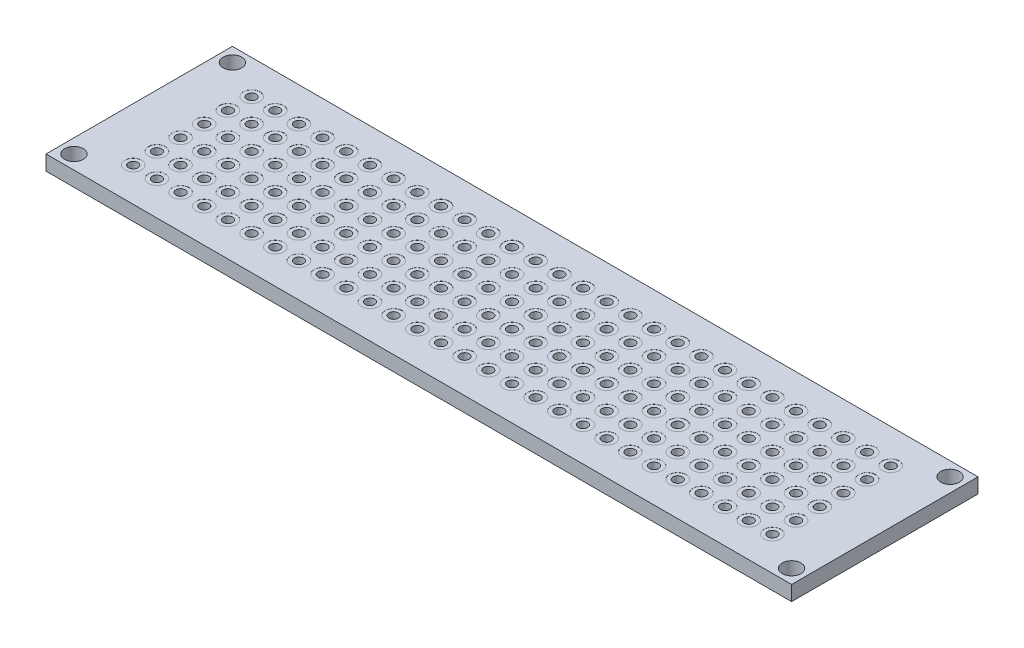
SolidWorks part; units mm, degrees
ref_plane "Front Plane" through (0, 0, 0) normal (0, 0, 1) x (1, 0, 0)
ref_plane "Top Plane" through (0, 0, 0) normal (0, 1, 0) x (1, 0, 0)
ref_plane "Right Plane" through (0, 0, 0) normal (1, 0, 0) x (0, 0, -1)
sketch "Sketch1" plane through (0, 0, 0) normal (0, 1, 0) x (1, 0, 0)
  line L0 (40, 0) -> (40, 20) construction
  line L1 (0, 0) -> (80, 0)
  line L2 (0, 0) -> (0, 20)
  line L3 (0, 20) -> (80, 20)
  line L4 (80, 0) -> (80, 20)
  line L5 (0, 10) -> (80, 10) construction
  circle A0 centre (5.71, 16.35) radius 0.5
  circle A1 centre (5.71, 13.81) radius 0.5
  circle A2 centre (5.71, 11.27) radius 0.5
  circle A3 centre (5.71, 8.73) radius 0.5
  circle A4 centre (5.71, 6.19) radius 0.5
  circle A5 centre (5.71, 3.65) radius 0.5
  circle A6 centre (8.25, 16.35) radius 0.5
  circle A7 centre (8.25, 13.81) radius 0.5
  circle A8 centre (8.25, 11.27) radius 0.5
  circle A9 centre (8.25, 8.73) radius 0.5
  circle A10 centre (8.25, 6.19) radius 0.5
  circle A11 centre (8.25, 3.65) radius 0.5
  circle A12 centre (10.79, 16.35) radius 0.5
  circle A13 centre (10.79, 13.81) radius 0.5
  circle A14 centre (10.79, 11.27) radius 0.5
  circle A15 centre (10.79, 8.73) radius 0.5
  circle A16 centre (10.79, 6.19) radius 0.5
  circle A17 centre (10.79, 3.65) radius 0.5
  circle A18 centre (13.33, 16.35) radius 0.5
  circle A19 centre (13.33, 13.81) radius 0.5
  circle A20 centre (13.33, 11.27) radius 0.5
  circle A21 centre (13.33, 8.73) radius 0.5
  circle A22 centre (13.33, 6.19) radius 0.5
  circle A23 centre (13.33, 3.65) radius 0.5
  circle A24 centre (15.87, 16.35) radius 0.5
  circle A25 centre (15.87, 13.81) radius 0.5
  circle A26 centre (15.87, 11.27) radius 0.5
  circle A27 centre (15.87, 8.73) radius 0.5
  circle A28 centre (15.87, 6.19) radius 0.5
  circle A29 centre (15.87, 3.65) radius 0.5
  circle A30 centre (18.41, 16.35) radius 0.5
  circle A31 centre (18.41, 13.81) radius 0.5
  circle A32 centre (18.41, 11.27) radius 0.5
  circle A33 centre (18.41, 8.73) radius 0.5
  circle A34 centre (18.41, 6.19) radius 0.5
  circle A35 centre (18.41, 3.65) radius 0.5
  circle A36 centre (20.95, 16.35) radius 0.5
  circle A37 centre (20.95, 13.81) radius 0.5
  circle A38 centre (20.95, 11.27) radius 0.5
  circle A39 centre (20.95, 8.73) radius 0.5
  circle A40 centre (20.95, 6.19) radius 0.5
  circle A41 centre (20.95, 3.65) radius 0.5
  circle A42 centre (23.49, 16.35) radius 0.5
  circle A43 centre (23.49, 13.81) radius 0.5
  circle A44 centre (23.49, 11.27) radius 0.5
  circle A45 centre (23.49, 8.73) radius 0.5
  circle A46 centre (23.49, 6.19) radius 0.5
  circle A47 centre (23.49, 3.65) radius 0.5
  circle A48 centre (26.03, 16.35) radius 0.5
  circle A49 centre (26.03, 13.81) radius 0.5
  circle A50 centre (26.03, 11.27) radius 0.5
  circle A51 centre (26.03, 8.73) radius 0.5
  circle A52 centre (26.03, 6.19) radius 0.5
  circle A53 centre (26.03, 3.65) radius 0.5
  circle A54 centre (28.57, 16.35) radius 0.5
  circle A55 centre (28.57, 13.81) radius 0.5
  circle A56 centre (28.57, 11.27) radius 0.5
  circle A57 centre (28.57, 8.73) radius 0.5
  circle A58 centre (28.57, 6.19) radius 0.5
  circle A59 centre (28.57, 3.65) radius 0.5
  circle A60 centre (31.11, 16.35) radius 0.5
  circle A61 centre (31.11, 13.81) radius 0.5
  circle A62 centre (31.11, 11.27) radius 0.5
  circle A63 centre (31.11, 8.73) radius 0.5
  circle A64 centre (31.11, 6.19) radius 0.5
  circle A65 centre (31.11, 3.65) radius 0.5
  circle A66 centre (33.65, 16.35) radius 0.5
  circle A67 centre (33.65, 13.81) radius 0.5
  circle A68 centre (33.65, 11.27) radius 0.5
  circle A69 centre (33.65, 8.73) radius 0.5
  circle A70 centre (33.65, 6.19) radius 0.5
  circle A71 centre (33.65, 3.65) radius 0.5
  circle A72 centre (36.19, 16.35) radius 0.5
  circle A73 centre (36.19, 13.81) radius 0.5
  circle A74 centre (36.19, 11.27) radius 0.5
  circle A75 centre (36.19, 8.73) radius 0.5
  circle A76 centre (36.19, 6.19) radius 0.5
  circle A77 centre (36.19, 3.65) radius 0.5
  circle A78 centre (38.73, 16.35) radius 0.5
  circle A79 centre (38.73, 13.81) radius 0.5
  circle A80 centre (38.73, 11.27) radius 0.5
  circle A81 centre (38.73, 8.73) radius 0.5
  circle A82 centre (38.73, 6.19) radius 0.5
  circle A83 centre (38.73, 3.65) radius 0.5
  circle A84 centre (41.27, 16.35) radius 0.5
  circle A85 centre (41.27, 13.81) radius 0.5
  circle A86 centre (41.27, 11.27) radius 0.5
  circle A87 centre (41.27, 8.73) radius 0.5
  circle A88 centre (41.27, 6.19) radius 0.5
  circle A89 centre (41.27, 3.65) radius 0.5
  circle A90 centre (43.81, 16.35) radius 0.5
  circle A91 centre (43.81, 13.81) radius 0.5
  circle A92 centre (43.81, 11.27) radius 0.5
  circle A93 centre (43.81, 8.73) radius 0.5
  circle A94 centre (43.81, 6.19) radius 0.5
  circle A95 centre (43.81, 3.65) radius 0.5
  circle A96 centre (46.35, 16.35) radius 0.5
  circle A97 centre (46.35, 13.81) radius 0.5
  circle A98 centre (46.35, 11.27) radius 0.5
  circle A99 centre (46.35, 8.73) radius 0.5
  circle A100 centre (46.35, 6.19) radius 0.5
  circle A101 centre (46.35, 3.65) radius 0.5
  circle A102 centre (48.89, 16.35) radius 0.5
  circle A103 centre (48.89, 13.81) radius 0.5
  circle A104 centre (48.89, 11.27) radius 0.5
  circle A105 centre (48.89, 8.73) radius 0.5
  circle A106 centre (48.89, 6.19) radius 0.5
  circle A107 centre (48.89, 3.65) radius 0.5
  circle A108 centre (51.43, 16.35) radius 0.5
  circle A109 centre (51.43, 13.81) radius 0.5
  circle A110 centre (51.43, 11.27) radius 0.5
  circle A111 centre (51.43, 8.73) radius 0.5
  circle A112 centre (51.43, 6.19) radius 0.5
  circle A113 centre (51.43, 3.65) radius 0.5
  circle A114 centre (53.97, 16.35) radius 0.5
  circle A115 centre (53.97, 13.81) radius 0.5
  circle A116 centre (53.97, 11.27) radius 0.5
  circle A117 centre (53.97, 8.73) radius 0.5
  circle A118 centre (53.97, 6.19) radius 0.5
  circle A119 centre (53.97, 3.65) radius 0.5
  circle A120 centre (56.51, 16.35) radius 0.5
  circle A121 centre (56.51, 13.81) radius 0.5
  circle A122 centre (56.51, 11.27) radius 0.5
  circle A123 centre (56.51, 8.73) radius 0.5
  circle A124 centre (56.51, 6.19) radius 0.5
  circle A125 centre (56.51, 3.65) radius 0.5
  circle A126 centre (59.05, 16.35) radius 0.5
  circle A127 centre (59.05, 13.81) radius 0.5
  circle A128 centre (59.05, 11.27) radius 0.5
  circle A129 centre (59.05, 8.73) radius 0.5
  circle A130 centre (59.05, 6.19) radius 0.5
  circle A131 centre (59.05, 3.65) radius 0.5
  circle A132 centre (61.59, 16.35) radius 0.5
  circle A133 centre (61.59, 13.81) radius 0.5
  circle A134 centre (61.59, 11.27) radius 0.5
  circle A135 centre (61.59, 8.73) radius 0.5
  circle A136 centre (61.59, 6.19) radius 0.5
  circle A137 centre (61.59, 3.65) radius 0.5
  circle A138 centre (64.13, 16.35) radius 0.5
  circle A139 centre (64.13, 13.81) radius 0.5
  circle A140 centre (64.13, 11.27) radius 0.5
  circle A141 centre (64.13, 8.73) radius 0.5
  circle A142 centre (64.13, 6.19) radius 0.5
  circle A143 centre (64.13, 3.65) radius 0.5
  circle A144 centre (66.67, 16.35) radius 0.5
  circle A145 centre (66.67, 13.81) radius 0.5
  circle A146 centre (66.67, 11.27) radius 0.5
  circle A147 centre (66.67, 8.73) radius 0.5
  circle A148 centre (66.67, 6.19) radius 0.5
  circle A149 centre (66.67, 3.65) radius 0.5
  circle A150 centre (69.21, 16.35) radius 0.5
  circle A151 centre (69.21, 13.81) radius 0.5
  circle A152 centre (69.21, 11.27) radius 0.5
  circle A153 centre (69.21, 8.73) radius 0.5
  circle A154 centre (69.21, 6.19) radius 0.5
  circle A155 centre (69.21, 3.65) radius 0.5
  circle A156 centre (71.75, 16.35) radius 0.5
  circle A157 centre (71.75, 13.81) radius 0.5
  circle A158 centre (71.75, 11.27) radius 0.5
  circle A159 centre (71.75, 8.73) radius 0.5
  circle A160 centre (71.75, 6.19) radius 0.5
  circle A161 centre (71.75, 3.65) radius 0.5
  circle A162 centre (74.29, 16.35) radius 0.5
  circle A163 centre (74.29, 13.81) radius 0.5
  circle A164 centre (74.29, 11.27) radius 0.5
  circle A165 centre (74.29, 8.73) radius 0.5
  circle A166 centre (74.29, 6.19) radius 0.5
  circle A167 centre (74.29, 3.65) radius 0.5
  circle A168 centre (1.5, 18.5) radius 1
  circle A169 centre (78.5, 18.5) radius 1
  circle A170 centre (1.5, 1.5) radius 1
  circle A171 centre (78.5, 1.5) radius 1
  dimension "D3" = 1
  dimension "D8" = 2
  dimension "D9" = 0.5
  dimension "D10" = 0.5
  dimension "D1" = 80
  dimension "D2" = 20
  dimension "D5" = 2.54
  dimension "D7" = 2.54
  dimension "D4" = 6
  dimension "D6" = 28
extrude "Boss-Extrude1" add sketch "Sketch1" along normal blind 1.6
sketch "Sketch2" plane through (0, 1.6, 0) normal (0, 1, 0) x (1, 0, 0)
  circle A0 centre (5.71, 16.35) radius 0.9
  circle A1 centre (8.25, 16.35) radius 0.9
  circle A2 centre (10.79, 16.35) radius 0.9
  circle A3 centre (13.33, 16.35) radius 0.9
  circle A4 centre (15.87, 16.35) radius 0.9
  circle A5 centre (18.41, 16.35) radius 0.9
  circle A6 centre (20.95, 16.35) radius 0.9
  circle A7 centre (23.49, 16.35) radius 0.9
  circle A8 centre (26.03, 16.35) radius 0.9
  circle A9 centre (28.57, 16.35) radius 0.9
  circle A10 centre (31.11, 16.35) radius 0.9
  circle A11 centre (33.65, 16.35) radius 0.9
  circle A12 centre (36.19, 16.35) radius 0.9
  circle A13 centre (38.73, 16.35) radius 0.9
  circle A14 centre (41.27, 16.35) radius 0.9
  circle A15 centre (43.81, 16.35) radius 0.9
  circle A16 centre (46.35, 16.35) radius 0.9
  circle A17 centre (48.89, 16.35) radius 0.9
  circle A18 centre (51.43, 16.35) radius 0.9
  circle A19 centre (53.97, 16.35) radius 0.9
  circle A20 centre (56.51, 16.35) radius 0.9
  circle A21 centre (59.05, 16.35) radius 0.9
  circle A22 centre (61.59, 16.35) radius 0.9
  circle A23 centre (64.13, 16.35) radius 0.9
  circle A24 centre (66.67, 16.35) radius 0.9
  circle A25 centre (69.21, 16.35) radius 0.9
  circle A26 centre (71.75, 16.35) radius 0.9
  circle A27 centre (74.29, 16.35) radius 0.9
  circle A28 centre (8.25, 13.81) radius 0.9
  circle A29 centre (10.79, 13.81) radius 0.9
  circle A30 centre (13.33, 13.81) radius 0.9
  circle A31 centre (15.87, 13.81) radius 0.9
  circle A32 centre (18.41, 13.81) radius 0.9
  circle A33 centre (20.95, 13.81) radius 0.9
  circle A34 centre (23.49, 13.81) radius 0.9
  circle A35 centre (26.03, 13.81) radius 0.9
  circle A36 centre (28.57, 13.81) radius 0.9
  circle A37 centre (31.11, 13.81) radius 0.9
  circle A38 centre (33.65, 13.81) radius 0.9
  circle A39 centre (36.19, 13.81) radius 0.9
  circle A40 centre (38.73, 13.81) radius 0.9
  circle A41 centre (41.27, 13.81) radius 0.9
  circle A42 centre (43.81, 13.81) radius 0.9
  circle A43 centre (46.35, 13.81) radius 0.9
  circle A44 centre (48.89, 13.81) radius 0.9
  circle A45 centre (51.43, 13.81) radius 0.9
  circle A46 centre (53.97, 13.81) radius 0.9
  circle A47 centre (56.51, 13.81) radius 0.9
  circle A48 centre (59.05, 13.81) radius 0.9
  circle A49 centre (61.59, 13.81) radius 0.9
  circle A50 centre (64.13, 13.81) radius 0.9
  circle A51 centre (66.67, 13.81) radius 0.9
  circle A52 centre (69.21, 13.81) radius 0.9
  circle A53 centre (71.75, 13.81) radius 0.9
  circle A54 centre (74.29, 13.81) radius 0.9
  circle A55 centre (8.25, 11.27) radius 0.9
  circle A56 centre (10.79, 11.27) radius 0.9
  circle A57 centre (13.33, 11.27) radius 0.9
  circle A58 centre (15.87, 11.27) radius 0.9
  circle A59 centre (18.41, 11.27) radius 0.9
  circle A60 centre (20.95, 11.27) radius 0.9
  circle A61 centre (23.49, 11.27) radius 0.9
  circle A62 centre (26.03, 11.27) radius 0.9
  circle A63 centre (28.57, 11.27) radius 0.9
  circle A64 centre (31.11, 11.27) radius 0.9
  circle A65 centre (33.65, 11.27) radius 0.9
  circle A66 centre (36.19, 11.27) radius 0.9
  circle A67 centre (38.73, 11.27) radius 0.9
  circle A68 centre (41.27, 11.27) radius 0.9
  circle A69 centre (43.81, 11.27) radius 0.9
  circle A70 centre (46.35, 11.27) radius 0.9
  circle A71 centre (48.89, 11.27) radius 0.9
  circle A72 centre (51.43, 11.27) radius 0.9
  circle A73 centre (53.97, 11.27) radius 0.9
  circle A74 centre (56.51, 11.27) radius 0.9
  circle A75 centre (59.05, 11.27) radius 0.9
  circle A76 centre (61.59, 11.27) radius 0.9
  circle A77 centre (64.13, 11.27) radius 0.9
  circle A78 centre (66.67, 11.27) radius 0.9
  circle A79 centre (69.21, 11.27) radius 0.9
  circle A80 centre (71.75, 11.27) radius 0.9
  circle A81 centre (74.29, 11.27) radius 0.9
  circle A82 centre (8.25, 8.73) radius 0.9
  circle A83 centre (10.79, 8.73) radius 0.9
  circle A84 centre (13.33, 8.73) radius 0.9
  circle A85 centre (15.87, 8.73) radius 0.9
  circle A86 centre (18.41, 8.73) radius 0.9
  circle A87 centre (20.95, 8.73) radius 0.9
  circle A88 centre (23.49, 8.73) radius 0.9
  circle A89 centre (26.03, 8.73) radius 0.9
  circle A90 centre (28.57, 8.73) radius 0.9
  circle A91 centre (31.11, 8.73) radius 0.9
  circle A92 centre (33.65, 8.73) radius 0.9
  circle A93 centre (36.19, 8.73) radius 0.9
  circle A94 centre (38.73, 8.73) radius 0.9
  circle A95 centre (41.27, 8.73) radius 0.9
  circle A96 centre (43.81, 8.73) radius 0.9
  circle A97 centre (46.35, 8.73) radius 0.9
  circle A98 centre (48.89, 8.73) radius 0.9
  circle A99 centre (51.43, 8.73) radius 0.9
  circle A100 centre (53.97, 8.73) radius 0.9
  circle A101 centre (56.51, 8.73) radius 0.9
  circle A102 centre (59.05, 8.73) radius 0.9
  circle A103 centre (61.59, 8.73) radius 0.9
  circle A104 centre (64.13, 8.73) radius 0.9
  circle A105 centre (66.67, 8.73) radius 0.9
  circle A106 centre (69.21, 8.73) radius 0.9
  circle A107 centre (71.75, 8.73) radius 0.9
  circle A108 centre (74.29, 8.73) radius 0.9
  circle A109 centre (8.25, 6.19) radius 0.9
  circle A110 centre (10.79, 6.19) radius 0.9
  circle A111 centre (13.33, 6.19) radius 0.9
  circle A112 centre (15.87, 6.19) radius 0.9
  circle A113 centre (18.41, 6.19) radius 0.9
  circle A114 centre (20.95, 6.19) radius 0.9
  circle A115 centre (23.49, 6.19) radius 0.9
  circle A116 centre (26.03, 6.19) radius 0.9
  circle A117 centre (28.57, 6.19) radius 0.9
  circle A118 centre (31.11, 6.19) radius 0.9
  circle A119 centre (33.65, 6.19) radius 0.9
  circle A120 centre (36.19, 6.19) radius 0.9
  circle A121 centre (38.73, 6.19) radius 0.9
  circle A122 centre (41.27, 6.19) radius 0.9
  circle A123 centre (43.81, 6.19) radius 0.9
  circle A124 centre (46.35, 6.19) radius 0.9
  circle A125 centre (48.89, 6.19) radius 0.9
  circle A126 centre (51.43, 6.19) radius 0.9
  circle A127 centre (53.97, 6.19) radius 0.9
  circle A128 centre (56.51, 6.19) radius 0.9
  circle A129 centre (59.05, 6.19) radius 0.9
  circle A130 centre (61.59, 6.19) radius 0.9
  circle A131 centre (64.13, 6.19) radius 0.9
  circle A132 centre (66.67, 6.19) radius 0.9
  circle A133 centre (69.21, 6.19) radius 0.9
  circle A134 centre (71.75, 6.19) radius 0.9
  circle A135 centre (74.29, 6.19) radius 0.9
  circle A136 centre (8.25, 3.65) radius 0.9
  circle A137 centre (10.79, 3.65) radius 0.9
  circle A138 centre (13.33, 3.65) radius 0.9
  circle A139 centre (15.87, 3.65) radius 0.9
  circle A140 centre (18.41, 3.65) radius 0.9
  circle A141 centre (20.95, 3.65) radius 0.9
  circle A142 centre (23.49, 3.65) radius 0.9
  circle A143 centre (26.03, 3.65) radius 0.9
  circle A144 centre (28.57, 3.65) radius 0.9
  circle A145 centre (31.11, 3.65) radius 0.9
  circle A146 centre (33.65, 3.65) radius 0.9
  circle A147 centre (36.19, 3.65) radius 0.9
  circle A148 centre (38.73, 3.65) radius 0.9
  circle A149 centre (41.27, 3.65) radius 0.9
  circle A150 centre (43.81, 3.65) radius 0.9
  circle A151 centre (46.35, 3.65) radius 0.9
  circle A152 centre (48.89, 3.65) radius 0.9
  circle A153 centre (51.43, 3.65) radius 0.9
  circle A154 centre (53.97, 3.65) radius 0.9
  circle A155 centre (56.51, 3.65) radius 0.9
  circle A156 centre (59.05, 3.65) radius 0.9
  circle A157 centre (61.59, 3.65) radius 0.9
  circle A158 centre (64.13, 3.65) radius 0.9
  circle A159 centre (66.67, 3.65) radius 0.9
  circle A160 centre (69.21, 3.65) radius 0.9
  circle A161 centre (71.75, 3.65) radius 0.9
  circle A162 centre (74.29, 3.65) radius 0.9
  circle A163 centre (5.71, 13.81) radius 0.9
  circle A164 centre (5.71, 11.27) radius 0.9
  circle A165 centre (5.71, 8.73) radius 0.9
  circle A166 centre (5.71, 6.19) radius 0.9
  circle A167 centre (5.71, 3.65) radius 0.9
  dimension "D1" = 1.8
  dimension "D2" = 28
  dimension "D3" = 6
extrude "Cut-Extrude1" cut sketch "Sketch2" against normal blind 0.01
sketch "Sketch3" plane through (0, 0, 0) normal (0, -1, 0) x (1, 0, 0)
  circle A1 centre (20.95, -3.65) radius 0.9
  circle A2 centre (20.95, -3.65) radius 0.9
  circle A3 centre (18.41, -3.65) radius 0.9
  circle A4 centre (18.41, -3.65) radius 0.9
  circle A5 centre (15.87, -3.65) radius 0.9
  circle A6 centre (15.87, -3.65) radius 0.9
  circle A7 centre (13.33, -3.65) radius 0.9
  circle A8 centre (13.33, -3.65) radius 0.9
  circle A9 centre (10.79, -3.65) radius 0.9
  circle A10 centre (10.79, -3.65) radius 0.9
  circle A11 centre (8.25, -3.65) radius 0.9
  circle A12 centre (8.25, -3.65) radius 0.9
  circle A13 centre (74.29, -6.19) radius 0.9
  circle A14 centre (74.29, -6.19) radius 0.9
  circle A15 centre (71.75, -6.19) radius 0.9
  circle A16 centre (71.75, -6.19) radius 0.9
  circle A17 centre (18.41, -16.35) radius 0.9
  circle A18 centre (18.41, -16.35) radius 0.9
  circle A19 centre (15.87, -16.35) radius 0.9
  circle A20 centre (15.87, -16.35) radius 0.9
  circle A21 centre (13.33, -16.35) radius 0.9
  circle A22 centre (13.33, -16.35) radius 0.9
  circle A23 centre (10.79, -16.35) radius 0.9
  circle A24 centre (10.79, -16.35) radius 0.9
  circle A25 centre (8.25, -16.35) radius 0.9
  circle A26 centre (8.25, -16.35) radius 0.9
  circle A27 centre (5.71, -16.35) radius 0.9
  circle A28 centre (5.71, -16.35) radius 0.9
  circle A29 centre (41.27, -3.65) radius 0.9
  circle A30 centre (41.27, -3.65) radius 0.9
  circle A31 centre (38.73, -3.65) radius 0.9
  circle A32 centre (38.73, -3.65) radius 0.9
  circle A33 centre (36.19, -3.65) radius 0.9
  circle A34 centre (36.19, -3.65) radius 0.9
  circle A35 centre (33.65, -3.65) radius 0.9
  circle A36 centre (33.65, -3.65) radius 0.9
  circle A37 centre (31.11, -3.65) radius 0.9
  circle A38 centre (31.11, -3.65) radius 0.9
  circle A39 centre (28.57, -3.65) radius 0.9
  circle A40 centre (28.57, -3.65) radius 0.9
  circle A41 centre (26.03, -3.65) radius 0.9
  circle A42 centre (26.03, -3.65) radius 0.9
  circle A43 centre (23.49, -3.65) radius 0.9
  circle A44 centre (23.49, -3.65) radius 0.9
  circle A45 centre (38.73, -16.35) radius 0.9
  circle A46 centre (38.73, -16.35) radius 0.9
  circle A47 centre (36.19, -16.35) radius 0.9
  circle A48 centre (36.19, -16.35) radius 0.9
  circle A49 centre (33.65, -16.35) radius 0.9
  circle A50 centre (33.65, -16.35) radius 0.9
  circle A51 centre (31.11, -16.35) radius 0.9
  circle A52 centre (31.11, -16.35) radius 0.9
  circle A53 centre (28.57, -16.35) radius 0.9
  circle A54 centre (28.57, -16.35) radius 0.9
  circle A55 centre (26.03, -16.35) radius 0.9
  circle A56 centre (26.03, -16.35) radius 0.9
  circle A57 centre (23.49, -16.35) radius 0.9
  circle A58 centre (23.49, -16.35) radius 0.9
  circle A59 centre (20.95, -16.35) radius 0.9
  circle A60 centre (20.95, -16.35) radius 0.9
  circle A61 centre (61.59, -3.65) radius 0.9
  circle A62 centre (61.59, -3.65) radius 0.9
  circle A63 centre (59.05, -3.65) radius 0.9
  circle A64 centre (59.05, -3.65) radius 0.9
  circle A65 centre (56.51, -3.65) radius 0.9
  circle A66 centre (56.51, -3.65) radius 0.9
  circle A67 centre (53.97, -3.65) radius 0.9
  circle A68 centre (53.97, -3.65) radius 0.9
  circle A69 centre (51.43, -3.65) radius 0.9
  circle A70 centre (51.43, -3.65) radius 0.9
  circle A71 centre (48.89, -3.65) radius 0.9
  circle A72 centre (48.89, -3.65) radius 0.9
  circle A73 centre (46.35, -3.65) radius 0.9
  circle A74 centre (46.35, -3.65) radius 0.9
  circle A75 centre (43.81, -3.65) radius 0.9
  circle A76 centre (43.81, -3.65) radius 0.9
  circle A77 centre (59.05, -16.35) radius 0.9
  circle A78 centre (59.05, -16.35) radius 0.9
  circle A79 centre (56.51, -16.35) radius 0.9
  circle A80 centre (56.51, -16.35) radius 0.9
  circle A81 centre (53.97, -16.35) radius 0.9
  circle A82 centre (53.97, -16.35) radius 0.9
  circle A83 centre (51.43, -16.35) radius 0.9
  circle A84 centre (51.43, -16.35) radius 0.9
  circle A85 centre (48.89, -16.35) radius 0.9
  circle A86 centre (48.89, -16.35) radius 0.9
  circle A87 centre (46.35, -16.35) radius 0.9
  circle A88 centre (46.35, -16.35) radius 0.9
  circle A89 centre (43.81, -16.35) radius 0.9
  circle A90 centre (43.81, -16.35) radius 0.9
  circle A91 centre (41.27, -16.35) radius 0.9
  circle A92 centre (41.27, -16.35) radius 0.9
  circle A93 centre (5.71, -8.73) radius 0.9
  circle A94 centre (5.71, -8.73) radius 0.9
  circle A95 centre (5.71, -11.27) radius 0.9
  circle A96 centre (5.71, -11.27) radius 0.9
  circle A97 centre (5.71, -13.81) radius 0.9
  circle A98 centre (5.71, -13.81) radius 0.9
  circle A99 centre (74.29, -3.65) radius 0.9
  circle A100 centre (74.29, -3.65) radius 0.9
  circle A101 centre (71.75, -3.65) radius 0.9
  circle A102 centre (71.75, -3.65) radius 0.9
  circle A103 centre (69.21, -3.65) radius 0.9
  circle A104 centre (69.21, -3.65) radius 0.9
  circle A105 centre (66.67, -3.65) radius 0.9
  circle A106 centre (66.67, -3.65) radius 0.9
  circle A107 centre (64.13, -3.65) radius 0.9
  circle A108 centre (64.13, -3.65) radius 0.9
  circle A109 centre (10.79, -13.81) radius 0.9
  circle A110 centre (10.79, -13.81) radius 0.9
  circle A111 centre (8.25, -13.81) radius 0.9
  circle A112 centre (8.25, -13.81) radius 0.9
  circle A113 centre (74.29, -16.35) radius 0.9
  circle A114 centre (74.29, -16.35) radius 0.9
  circle A115 centre (71.75, -16.35) radius 0.9
  circle A116 centre (71.75, -16.35) radius 0.9
  circle A117 centre (69.21, -16.35) radius 0.9
  circle A118 centre (69.21, -16.35) radius 0.9
  circle A119 centre (66.67, -16.35) radius 0.9
  circle A120 centre (66.67, -16.35) radius 0.9
  circle A121 centre (64.13, -16.35) radius 0.9
  circle A122 centre (64.13, -16.35) radius 0.9
  circle A123 centre (61.59, -16.35) radius 0.9
  circle A124 centre (61.59, -16.35) radius 0.9
  circle A125 centre (5.71, -3.65) radius 0.9
  circle A126 centre (5.71, -3.65) radius 0.9
  circle A127 centre (5.71, -6.19) radius 0.9
  circle A128 centre (5.71, -6.19) radius 0.9
  circle A129 centre (31.11, -13.81) radius 0.9
  circle A130 centre (31.11, -13.81) radius 0.9
  circle A131 centre (28.57, -13.81) radius 0.9
  circle A132 centre (28.57, -13.81) radius 0.9
  circle A133 centre (26.03, -13.81) radius 0.9
  circle A134 centre (26.03, -13.81) radius 0.9
  circle A135 centre (23.49, -13.81) radius 0.9
  circle A136 centre (23.49, -13.81) radius 0.9
  circle A137 centre (20.95, -13.81) radius 0.9
  circle A138 centre (20.95, -13.81) radius 0.9
  circle A139 centre (18.41, -13.81) radius 0.9
  circle A140 centre (18.41, -13.81) radius 0.9
  circle A141 centre (15.87, -13.81) radius 0.9
  circle A142 centre (15.87, -13.81) radius 0.9
  circle A143 centre (13.33, -13.81) radius 0.9
  circle A144 centre (13.33, -13.81) radius 0.9
  circle A145 centre (51.43, -13.81) radius 0.9
  circle A146 centre (51.43, -13.81) radius 0.9
  circle A147 centre (48.89, -13.81) radius 0.9
  circle A148 centre (48.89, -13.81) radius 0.9
  circle A149 centre (46.35, -13.81) radius 0.9
  circle A150 centre (46.35, -13.81) radius 0.9
  circle A151 centre (43.81, -13.81) radius 0.9
  circle A152 centre (43.81, -13.81) radius 0.9
  circle A153 centre (41.27, -13.81) radius 0.9
  circle A154 centre (41.27, -13.81) radius 0.9
  circle A155 centre (38.73, -13.81) radius 0.9
  circle A156 centre (38.73, -13.81) radius 0.9
  circle A157 centre (36.19, -13.81) radius 0.9
  circle A158 centre (36.19, -13.81) radius 0.9
  circle A159 centre (33.65, -13.81) radius 0.9
  circle A160 centre (33.65, -13.81) radius 0.9
  circle A161 centre (71.75, -13.81) radius 0.9
  circle A162 centre (71.75, -13.81) radius 0.9
  circle A163 centre (69.21, -13.81) radius 0.9
  circle A164 centre (69.21, -13.81) radius 0.9
  circle A165 centre (66.67, -13.81) radius 0.9
  circle A166 centre (66.67, -13.81) radius 0.9
  circle A167 centre (64.13, -13.81) radius 0.9
  circle A168 centre (64.13, -13.81) radius 0.9
  circle A169 centre (61.59, -13.81) radius 0.9
  circle A170 centre (61.59, -13.81) radius 0.9
  circle A171 centre (59.05, -13.81) radius 0.9
  circle A172 centre (59.05, -13.81) radius 0.9
  circle A173 centre (56.51, -13.81) radius 0.9
  circle A174 centre (56.51, -13.81) radius 0.9
  circle A175 centre (53.97, -13.81) radius 0.9
  circle A176 centre (53.97, -13.81) radius 0.9
  circle A177 centre (23.49, -11.27) radius 0.9
  circle A178 centre (23.49, -11.27) radius 0.9
  circle A179 centre (20.95, -11.27) radius 0.9
  circle A180 centre (20.95, -11.27) radius 0.9
  circle A181 centre (18.41, -11.27) radius 0.9
  circle A182 centre (18.41, -11.27) radius 0.9
  circle A183 centre (15.87, -11.27) radius 0.9
  circle A184 centre (15.87, -11.27) radius 0.9
  circle A185 centre (13.33, -11.27) radius 0.9
  circle A186 centre (13.33, -11.27) radius 0.9
  circle A187 centre (10.79, -11.27) radius 0.9
  circle A188 centre (10.79, -11.27) radius 0.9
  circle A189 centre (8.25, -11.27) radius 0.9
  circle A190 centre (8.25, -11.27) radius 0.9
  circle A191 centre (74.29, -13.81) radius 0.9
  circle A192 centre (74.29, -13.81) radius 0.9
  circle A193 centre (43.81, -11.27) radius 0.9
  circle A194 centre (43.81, -11.27) radius 0.9
  circle A195 centre (41.27, -11.27) radius 0.9
  circle A196 centre (41.27, -11.27) radius 0.9
  circle A197 centre (38.73, -11.27) radius 0.9
  circle A198 centre (38.73, -11.27) radius 0.9
  circle A199 centre (36.19, -11.27) radius 0.9
  circle A200 centre (36.19, -11.27) radius 0.9
  circle A201 centre (33.65, -11.27) radius 0.9
  circle A202 centre (33.65, -11.27) radius 0.9
  circle A203 centre (31.11, -11.27) radius 0.9
  circle A204 centre (31.11, -11.27) radius 0.9
  circle A205 centre (28.57, -11.27) radius 0.9
  circle A206 centre (28.57, -11.27) radius 0.9
  circle A207 centre (26.03, -11.27) radius 0.9
  circle A208 centre (26.03, -11.27) radius 0.9
  circle A209 centre (64.13, -11.27) radius 0.9
  circle A210 centre (64.13, -11.27) radius 0.9
  circle A211 centre (61.59, -11.27) radius 0.9
  circle A212 centre (61.59, -11.27) radius 0.9
  circle A213 centre (59.05, -11.27) radius 0.9
  circle A214 centre (59.05, -11.27) radius 0.9
  circle A215 centre (56.51, -11.27) radius 0.9
  circle A216 centre (56.51, -11.27) radius 0.9
  circle A217 centre (53.97, -11.27) radius 0.9
  circle A218 centre (53.97, -11.27) radius 0.9
  circle A219 centre (51.43, -11.27) radius 0.9
  circle A220 centre (51.43, -11.27) radius 0.9
  circle A221 centre (48.89, -11.27) radius 0.9
  circle A222 centre (48.89, -11.27) radius 0.9
  circle A223 centre (46.35, -11.27) radius 0.9
  circle A224 centre (46.35, -11.27) radius 0.9
  circle A225 centre (15.87, -8.73) radius 0.9
  circle A226 centre (15.87, -8.73) radius 0.9
  circle A227 centre (13.33, -8.73) radius 0.9
  circle A228 centre (13.33, -8.73) radius 0.9
  circle A229 centre (10.79, -8.73) radius 0.9
  circle A230 centre (10.79, -8.73) radius 0.9
  circle A231 centre (8.25, -8.73) radius 0.9
  circle A232 centre (8.25, -8.73) radius 0.9
  circle A233 centre (74.29, -11.27) radius 0.9
  circle A234 centre (74.29, -11.27) radius 0.9
  circle A235 centre (71.75, -11.27) radius 0.9
  circle A236 centre (71.75, -11.27) radius 0.9
  circle A237 centre (69.21, -11.27) radius 0.9
  circle A238 centre (69.21, -11.27) radius 0.9
  circle A239 centre (66.67, -11.27) radius 0.9
  circle A240 centre (66.67, -11.27) radius 0.9
  circle A241 centre (36.19, -8.73) radius 0.9
  circle A242 centre (36.19, -8.73) radius 0.9
  circle A243 centre (33.65, -8.73) radius 0.9
  circle A244 centre (33.65, -8.73) radius 0.9
  circle A245 centre (31.11, -8.73) radius 0.9
  circle A246 centre (31.11, -8.73) radius 0.9
  circle A247 centre (28.57, -8.73) radius 0.9
  circle A248 centre (28.57, -8.73) radius 0.9
  circle A249 centre (26.03, -8.73) radius 0.9
  circle A250 centre (26.03, -8.73) radius 0.9
  circle A251 centre (23.49, -8.73) radius 0.9
  circle A252 centre (23.49, -8.73) radius 0.9
  circle A253 centre (20.95, -8.73) radius 0.9
  circle A254 centre (20.95, -8.73) radius 0.9
  circle A255 centre (18.41, -8.73) radius 0.9
  circle A256 centre (18.41, -8.73) radius 0.9
  circle A257 centre (56.51, -8.73) radius 0.9
  circle A258 centre (56.51, -8.73) radius 0.9
  circle A259 centre (53.97, -8.73) radius 0.9
  circle A260 centre (53.97, -8.73) radius 0.9
  circle A261 centre (51.43, -8.73) radius 0.9
  circle A262 centre (51.43, -8.73) radius 0.9
  circle A263 centre (48.89, -8.73) radius 0.9
  circle A264 centre (48.89, -8.73) radius 0.9
  circle A265 centre (46.35, -8.73) radius 0.9
  circle A266 centre (46.35, -8.73) radius 0.9
  circle A267 centre (43.81, -8.73) radius 0.9
  circle A268 centre (43.81, -8.73) radius 0.9
  circle A269 centre (41.27, -8.73) radius 0.9
  circle A270 centre (41.27, -8.73) radius 0.9
  circle A271 centre (38.73, -8.73) radius 0.9
  circle A272 centre (38.73, -8.73) radius 0.9
  circle A273 centre (8.25, -6.19) radius 0.9
  circle A274 centre (8.25, -6.19) radius 0.9
  circle A275 centre (74.29, -8.73) radius 0.9
  circle A276 centre (74.29, -8.73) radius 0.9
  circle A277 centre (71.75, -8.73) radius 0.9
  circle A278 centre (71.75, -8.73) radius 0.9
  circle A279 centre (69.21, -8.73) radius 0.9
  circle A280 centre (69.21, -8.73) radius 0.9
  circle A281 centre (66.67, -8.73) radius 0.9
  circle A282 centre (66.67, -8.73) radius 0.9
  circle A283 centre (64.13, -8.73) radius 0.9
  circle A284 centre (64.13, -8.73) radius 0.9
  circle A285 centre (61.59, -8.73) radius 0.9
  circle A286 centre (61.59, -8.73) radius 0.9
  circle A287 centre (59.05, -8.73) radius 0.9
  circle A288 centre (59.05, -8.73) radius 0.9
  circle A289 centre (28.57, -6.19) radius 0.9
  circle A290 centre (28.57, -6.19) radius 0.9
  circle A291 centre (26.03, -6.19) radius 0.9
  circle A292 centre (26.03, -6.19) radius 0.9
  circle A293 centre (23.49, -6.19) radius 0.9
  circle A294 centre (23.49, -6.19) radius 0.9
  circle A295 centre (20.95, -6.19) radius 0.9
  circle A296 centre (20.95, -6.19) radius 0.9
  circle A297 centre (18.41, -6.19) radius 0.9
  circle A298 centre (18.41, -6.19) radius 0.9
  circle A299 centre (15.87, -6.19) radius 0.9
  circle A300 centre (15.87, -6.19) radius 0.9
  circle A301 centre (13.33, -6.19) radius 0.9
  circle A302 centre (13.33, -6.19) radius 0.9
  circle A303 centre (10.79, -6.19) radius 0.9
  circle A304 centre (10.79, -6.19) radius 0.9
  circle A305 centre (48.89, -6.19) radius 0.9
  circle A306 centre (48.89, -6.19) radius 0.9
  circle A307 centre (46.35, -6.19) radius 0.9
  circle A308 centre (46.35, -6.19) radius 0.9
  circle A309 centre (43.81, -6.19) radius 0.9
  circle A310 centre (43.81, -6.19) radius 0.9
  circle A311 centre (41.27, -6.19) radius 0.9
  circle A312 centre (41.27, -6.19) radius 0.9
  circle A313 centre (38.73, -6.19) radius 0.9
  circle A314 centre (38.73, -6.19) radius 0.9
  circle A315 centre (36.19, -6.19) radius 0.9
  circle A316 centre (36.19, -6.19) radius 0.9
  circle A317 centre (33.65, -6.19) radius 0.9
  circle A318 centre (33.65, -6.19) radius 0.9
  circle A319 centre (31.11, -6.19) radius 0.9
  circle A320 centre (31.11, -6.19) radius 0.9
  circle A321 centre (69.21, -6.19) radius 0.9
  circle A322 centre (69.21, -6.19) radius 0.9
  circle A323 centre (66.67, -6.19) radius 0.9
  circle A324 centre (66.67, -6.19) radius 0.9
  circle A325 centre (64.13, -6.19) radius 0.9
  circle A326 centre (64.13, -6.19) radius 0.9
  circle A327 centre (61.59, -6.19) radius 0.9
  circle A328 centre (61.59, -6.19) radius 0.9
  circle A329 centre (59.05, -6.19) radius 0.9
  circle A330 centre (59.05, -6.19) radius 0.9
  circle A331 centre (56.51, -6.19) radius 0.9
  circle A332 centre (56.51, -6.19) radius 0.9
  circle A333 centre (53.97, -6.19) radius 0.9
  circle A334 centre (53.97, -6.19) radius 0.9
  circle A335 centre (51.43, -6.19) radius 0.9
  circle A336 centre (51.43, -6.19) radius 0.9
  dimension "D1" = 0
  dimension "D2" = 0
  dimension "D3" = 0
  dimension "D4" = 0
  dimension "D5" = 0
  dimension "D6" = 0
  dimension "D7" = 0
  dimension "D8" = 0
  dimension "D9" = 0
  dimension "D10" = 0
  dimension "D11" = 0
  dimension "D12" = 0
  dimension "D13" = 0
  dimension "D14" = 0
  dimension "D15" = 0
  dimension "D16" = 0
  dimension "D17" = 0
  dimension "D18" = 0
  dimension "D19" = 0
  dimension "D20" = 0
  dimension "D21" = 0
  dimension "D22" = 0
  dimension "D23" = 0
  dimension "D24" = 0
  dimension "D25" = 0
  dimension "D26" = 0
  dimension "D27" = 0
  dimension "D28" = 0
  dimension "D29" = 0
  dimension "D30" = 0
  dimension "D31" = 0
  dimension "D32" = 0
  dimension "D33" = 0
  dimension "D34" = 0
  dimension "D35" = 0
  dimension "D36" = 0
  dimension "D37" = 0
  dimension "D38" = 0
  dimension "D39" = 0
  dimension "D40" = 0
  dimension "D41" = 0
  dimension "D42" = 0
  dimension "D43" = 0
  dimension "D44" = 0
  dimension "D45" = 0
  dimension "D46" = 0
  dimension "D47" = 0
  dimension "D48" = 0
  dimension "D49" = 0
  dimension "D50" = 0
  dimension "D51" = 0
  dimension "D52" = 0
  dimension "D53" = 0
  dimension "D54" = 0
  dimension "D55" = 0
  dimension "D56" = 0
  dimension "D57" = 0
  dimension "D58" = 0
  dimension "D59" = 0
  dimension "D60" = 0
  dimension "D61" = 0
  dimension "D62" = 0
  dimension "D63" = 0
  dimension "D64" = 0
  dimension "D65" = 0
  dimension "D66" = 0
  dimension "D67" = 0
  dimension "D68" = 0
  dimension "D69" = 0
  dimension "D70" = 0
  dimension "D71" = 0
  dimension "D72" = 0
  dimension "D73" = 0
  dimension "D74" = 0
  dimension "D75" = 0
  dimension "D76" = 0
  dimension "D77" = 0
  dimension "D78" = 0
  dimension "D79" = 0
  dimension "D80" = 0
  dimension "D81" = 0
  dimension "D82" = 0
  dimension "D83" = 0
  dimension "D84" = 0
  dimension "D85" = 0
  dimension "D86" = 0
  dimension "D87" = 0
  dimension "D88" = 0
  dimension "D89" = 0
  dimension "D90" = 0
  dimension "D91" = 0
  dimension "D92" = 0
  dimension "D93" = 0
  dimension "D94" = 0
  dimension "D95" = 0
  dimension "D96" = 0
  dimension "D97" = 0
  dimension "D98" = 0
  dimension "D99" = 0
  dimension "D100" = 0
  dimension "D101" = 0
  dimension "D102" = 0
  dimension "D103" = 0
  dimension "D104" = 0
  dimension "D105" = 0
  dimension "D106" = 0
  dimension "D107" = 0
  dimension "D108" = 0
  dimension "D109" = 0
  dimension "D110" = 0
  dimension "D111" = 0
  dimension "D112" = 0
  dimension "D113" = 0
  dimension "D114" = 0
  dimension "D115" = 0
  dimension "D116" = 0
  dimension "D117" = 0
  dimension "D118" = 0
  dimension "D119" = 0
  dimension "D120" = 0
  dimension "D121" = 0
  dimension "D122" = 0
  dimension "D123" = 0
  dimension "D124" = 0
  dimension "D125" = 0
  dimension "D126" = 0
  dimension "D127" = 0
  dimension "D128" = 0
  dimension "D129" = 0
  dimension "D130" = 0
  dimension "D131" = 0
  dimension "D132" = 0
  dimension "D133" = 0
  dimension "D134" = 0
  dimension "D135" = 0
  dimension "D136" = 0
  dimension "D137" = 0
  dimension "D138" = 0
  dimension "D139" = 0
  dimension "D140" = 0
  dimension "D141" = 0
  dimension "D142" = 0
  dimension "D143" = 0
  dimension "D144" = 0
  dimension "D145" = 0
  dimension "D146" = 0
  dimension "D147" = 0
  dimension "D148" = 0
  dimension "D149" = 0
  dimension "D150" = 0
  dimension "D151" = 0
  dimension "D152" = 0
  dimension "D153" = 0
  dimension "D154" = 0
  dimension "D155" = 0
  dimension "D156" = 0
  dimension "D157" = 0
  dimension "D158" = 0
  dimension "D159" = 0
  dimension "D160" = 0
  dimension "D161" = 0
  dimension "D162" = 0
  dimension "D163" = 0
  dimension "D164" = 0
  dimension "D165" = 0
  dimension "D166" = 0
  dimension "D167" = 0
  dimension "D168" = 0
extrude "Cut-Extrude2" cut sketch "Sketch3" against normal blind 0.01
